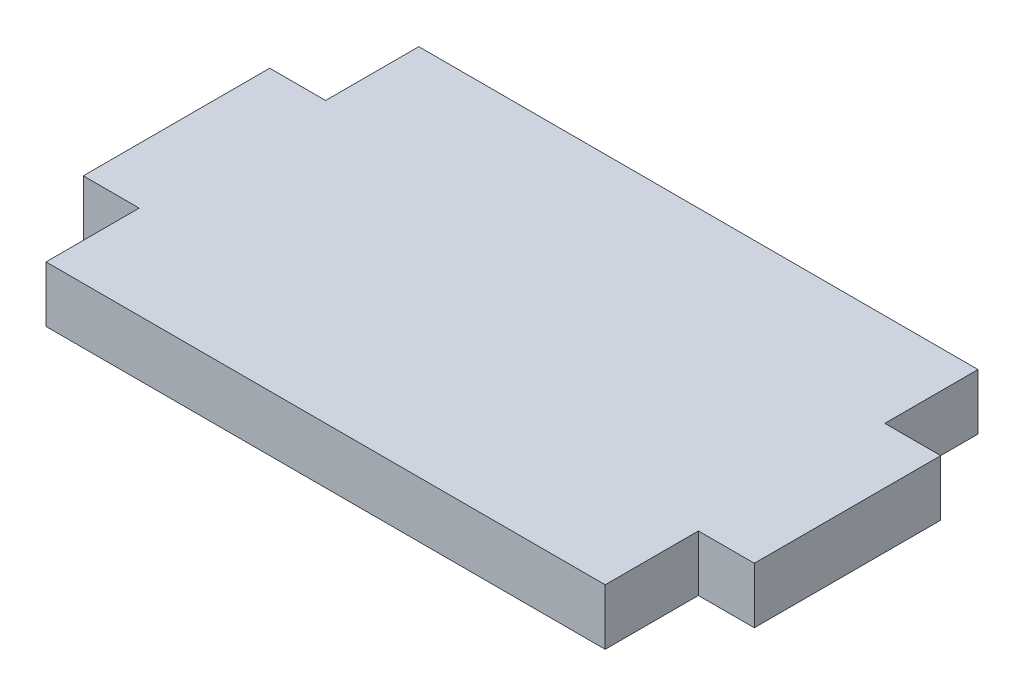
SolidWorks part; units mm, degrees
ref_plane "Front Plane" through (0, 0, 0) normal (0, 0, 1) x (1, 0, 0)
ref_plane "Top Plane" through (0, 0, 0) normal (0, 1, 0) x (1, 0, 0)
ref_plane "Right Plane" through (0, 0, 0) normal (1, 0, 0) x (0, 0, -1)
sketch "Sketch1" plane through (0, 0, 0) normal (0, 1, 0) x (1, 0, 0)
  line L0 (-15, 10) -> (-15, 5)
  line L1 (15, 10) -> (-15, 10)
  line L2 (-15, 5) -> (-18, 5)
  line L3 (15, -10) -> (-15, -10)
  line L4 (-18, 5) -> (-18, -5)
  line L5 (15, 10) -> (-15, -10) construction
  line L6 (15, -10) -> (-15, 10) construction
  line L7 (-18, -5) -> (-15, -5)
  line L8 (-15, -5) -> (-15, -10)
  line L9 (15, -10) -> (15, -5)
  line L10 (15, -5) -> (18, -5)
  line L11 (18, -5) -> (18, 5)
  line L12 (18, 5) -> (15, 5)
  line L13 (15, 5) -> (15, 10)
  point P0 (0, 0)
  dimension "D1" = 30
  dimension "D2" = 20
  dimension "D3" = 5
  dimension "D4" = 3
extrude "Boss-Extrude1" add sketch "Sketch1" along normal blind 3
